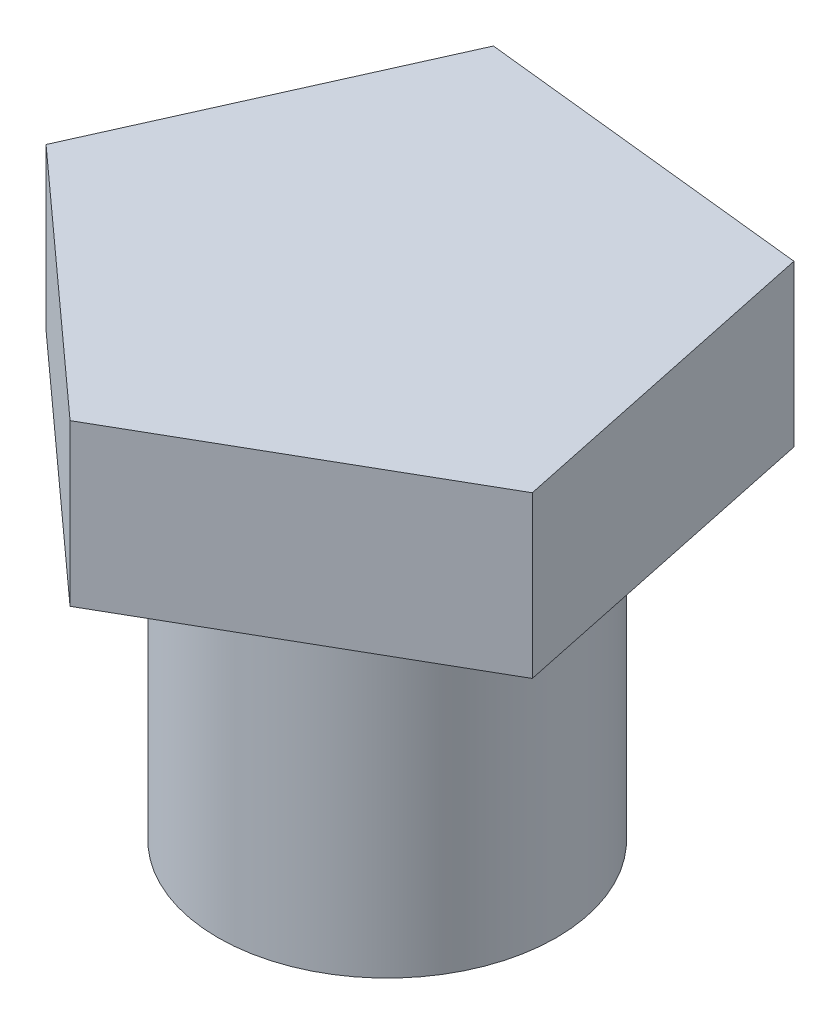
SolidWorks part; units mm, degrees
ref_plane "Front Plane" through (0, 0, 0) normal (0, 0, 1) x (1, 0, 0)
ref_plane "Top Plane" through (0, 0, 0) normal (0, 1, 0) x (1, 0, 0)
ref_plane "Right Plane" through (0, 0, 0) normal (1, 0, 0) x (0, 0, -1)
sketch "Sketch1" plane through (0, 0, 0) normal (0, 1, 0) x (1, 0, 0)
  circle A0 centre (0, 0) radius 5.08
  dimension "D1" = 10.16
extrude "Boss-Extrude1" add sketch "Sketch1" along normal blind 9.906
sketch "Sketch2" plane through (0, 9.906, 0) normal (0, 1, 0) x (1, 0, 0)
  line L1 (7.8877, -3.5324) -> (5.797, 6.4101)
  line L2 (5.797, 6.4101) -> (-4.305, 7.4941)
  line L3 (-4.305, 7.4941) -> (-8.4576, -1.7785)
  line L4 (-8.4576, -1.7785) -> (-0.9221, -8.5933)
  line L5 (-0.9221, -8.5933) -> (7.8877, -3.5324)
  circle A0 centre (0, 0) radius 6.992 construction
  dimension "D1" = 10.16
extrude "Boss-Extrude2" add sketch "Sketch2" along normal blind 4.826
